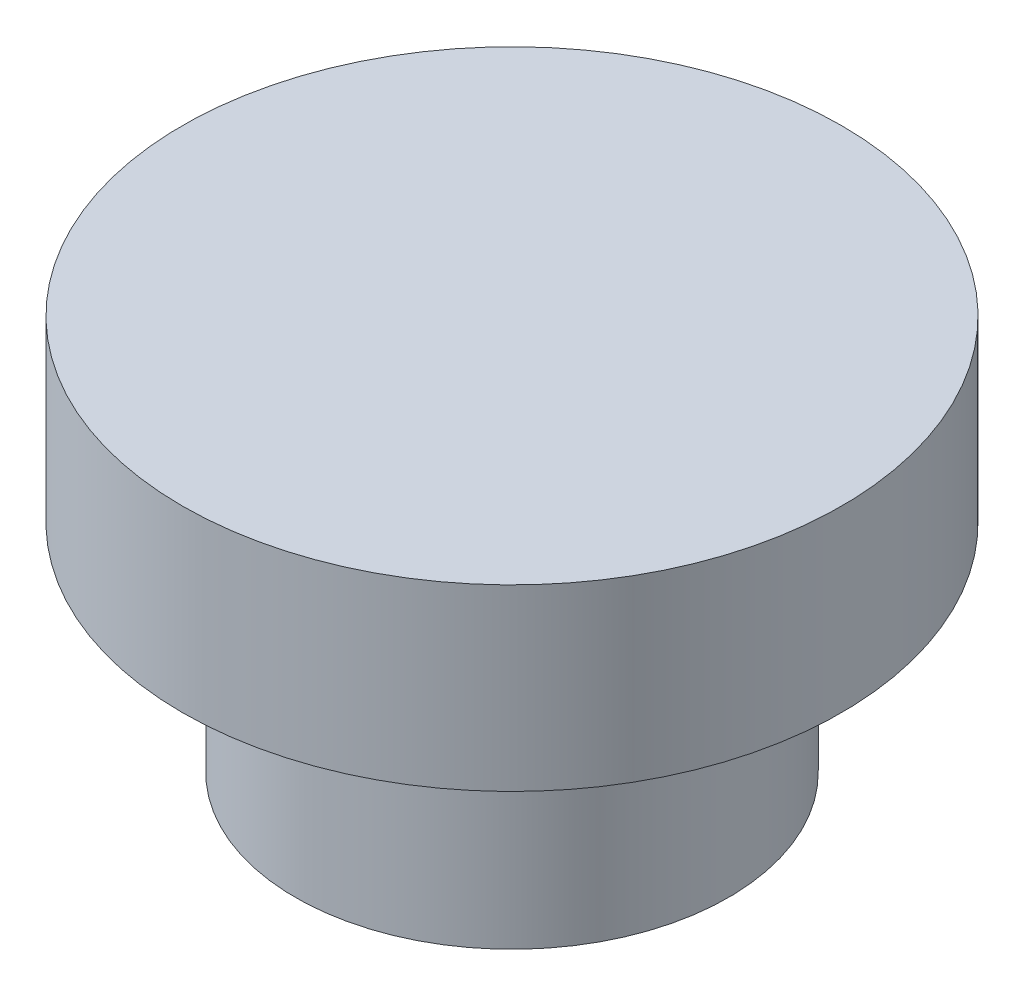
SolidWorks part; units mm, degrees
ref_plane "Front Plane" through (0, 0, 0) normal (0, 0, 1) x (1, 0, 0)
ref_plane "Top Plane" through (0, 0, 0) normal (0, 1, 0) x (1, 0, 0)
ref_plane "Right Plane" through (0, 0, 0) normal (1, 0, 0) x (0, 0, -1)
sketch "Sketch1" plane through (0, 0, 0) normal (0, 0, 1) x (1, 0, 0)
  line L0 (0, 0) -> (0, 5.334)
  line L1 (0, 5.334) -> (4.445, 5.334)
  line L2 (4.445, 5.334) -> (4.445, 2.921)
  line L3 (4.445, 2.921) -> (2.921, 2.921)
  line L4 (2.921, 2.921) -> (2.921, 0)
  line L5 (2.921, 0) -> (0, 0)
  dimension "D1" = 5.334
  dimension "D2" = 4.445
  dimension "D3" = 2.921
  dimension "D4" = 2.413
revolve "Revolve1" add sketch "Sketch1" angle 360 about L0
